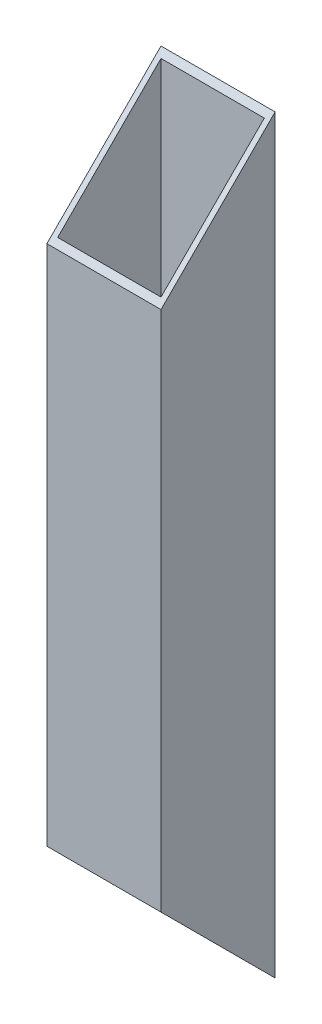
SolidWorks part; units mm, degrees
ref_plane "Alzado" through (0, 0, 0) normal (0, 0, 1) x (1, 0, 0)
ref_plane "Planta" through (0, 0, 0) normal (0, 1, 0) x (1, 0, 0)
ref_plane "Vista lateral" through (0, 0, 0) normal (1, 0, 0) x (0, 0, -1)
sketch "Sketch1" plane through (0, 0, 0) normal (0, 1, 0) x (1, 0, 0)
  line L0 (0, 0) -> (25.4, 0)
  line L1 (25.4, 0) -> (25.4, 25.4)
  line L2 (25.4, 25.4) -> (0, 25.4)
  line L3 (0, 25.4) -> (0, 0)
  line L4 (1.2, 24.2) -> (1.2, 1.2)
  line L5 (1.2, 1.2) -> (24.2, 1.2)
  line L6 (24.2, 1.2) -> (24.2, 24.2)
  line L7 (24.2, 24.2) -> (1.2, 24.2)
  dimension "D1" = 25.4
  dimension "D2" = 25.4
  dimension "D3" = 1.2
  dimension "D4" = 1.2
  dimension "D5" = 1.2
  dimension "D6" = 1.2
extrude "Boss-Extrude1" add sketch "Sketch1" along normal blind 166.94
sketch "Sketch2" plane through (25.4, 0, 0) normal (1, 0, 0) x (0, 0, -1)
  line L0 (25.4, 166.94) -> (0, 166.94)
  line L1 (0, 166.94) -> (0, 0) construction
  line L2 (0, 166.94) -> (25.4, 166.94) construction
  line L3 (0, 166.94) -> (0, 141.54)
  line L4 (0, 141.54) -> (25.4, 166.94)
  line L5 (0, 0) -> (0, 25.4)
  line L6 (0, 25.4) -> (25.4, 0)
  line L7 (25.4, 0) -> (0, 0)
  dimension "D1" = 25.4
  dimension "D2" = 25.4
extrude "Cut-Extrude1" cut sketch "Sketch2" against normal through all
